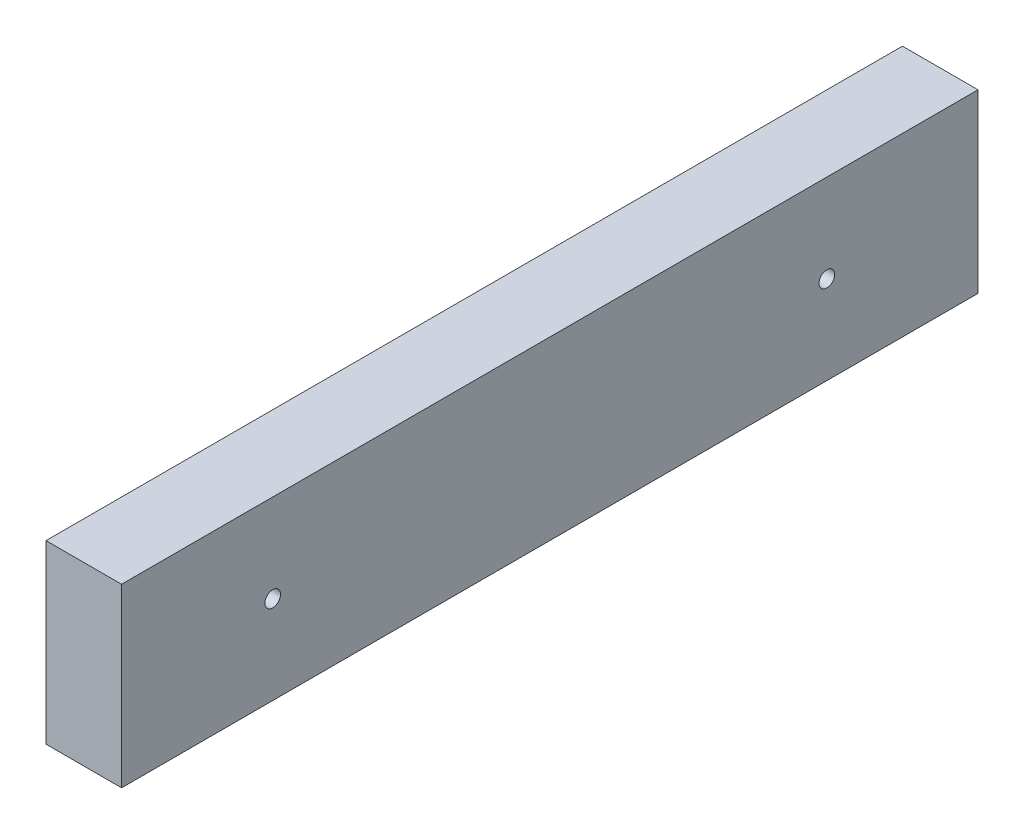
SolidWorks part; units mm, degrees
material "Pine"
ref_plane "Front Plane" through (0, 0, 0) normal (0, 0, 1) x (1, 0, 0)
ref_plane "Top Plane" through (0, 0, 0) normal (0, 1, 0) x (1, 0, 0)
ref_plane "Right Plane" through (0, 0, 0) normal (1, 0, 0) x (0, 0, -1)
sketch "Sketch1" plane through (0, 0, 0) normal (0, 0, 1) x (1, 0, 0)
  line L1 (-19.05, -44.45) -> (19.05, -44.45)
  line L2 (-19.05, -44.45) -> (-19.05, 44.45)
  line L3 (-19.05, 44.45) -> (19.05, 44.45)
  line L4 (19.05, -44.45) -> (19.05, 44.45)
  line L5 (-19.05, -44.45) -> (19.05, 44.45) construction
  line L6 (-19.05, 44.45) -> (19.05, -44.45) construction
  point P0 (0, 0)
  dimension "D1" = 88.9
  dimension "D2" = 38.1
extrude "Boss-Extrude1" add sketch "Sketch1" along normal blind 431.8
sketch "Sketch2" plane through (19.05, 0, 0) normal (1, 0, 0) x (0, 0, -1)
  line L0 (-431.8, -44.45) -> (-431.8, 44.45) construction
  line L1 (0, -44.45) -> (0, 44.45) construction
  point P0 (-355.6, 0)
  point P1 (-76.2, 0)
  dimension "D1" = 76.2
  dimension "D2" = 76.2
hole_wizard "5/16 (0.3125) Diameter Hole1" positions "Sketch3" profile "Sketch4" hole size "5/16" standard "ANSI Inch" end condition through all
sketch "Sketch3" plane through (19.05, 0, 0) normal (1, 0, 0) x (0, 0, -1)
  point P0 (-355.6, 0)
  point P3 (-76.2, 0)
sketch "Sketch4" plane through (19.05, 0, 355.6) normal (0, 1, 0) x (0, 0, -1)
  line L0 (0, 0) -> (0, 38.1)
  line L1 (0, 38.1) -> (3.9687, 38.1)
  line L2 (3.9687, 38.1) -> (3.9687, 0)
  line L5 (3.9687, 0) -> (0, 0)
  line L11 (0, -6.35) -> (0, 107.95) construction
  dimension "Thru Hole Dia." = 7.9375
  dimension "Thru Hole Depth" = 38.1
